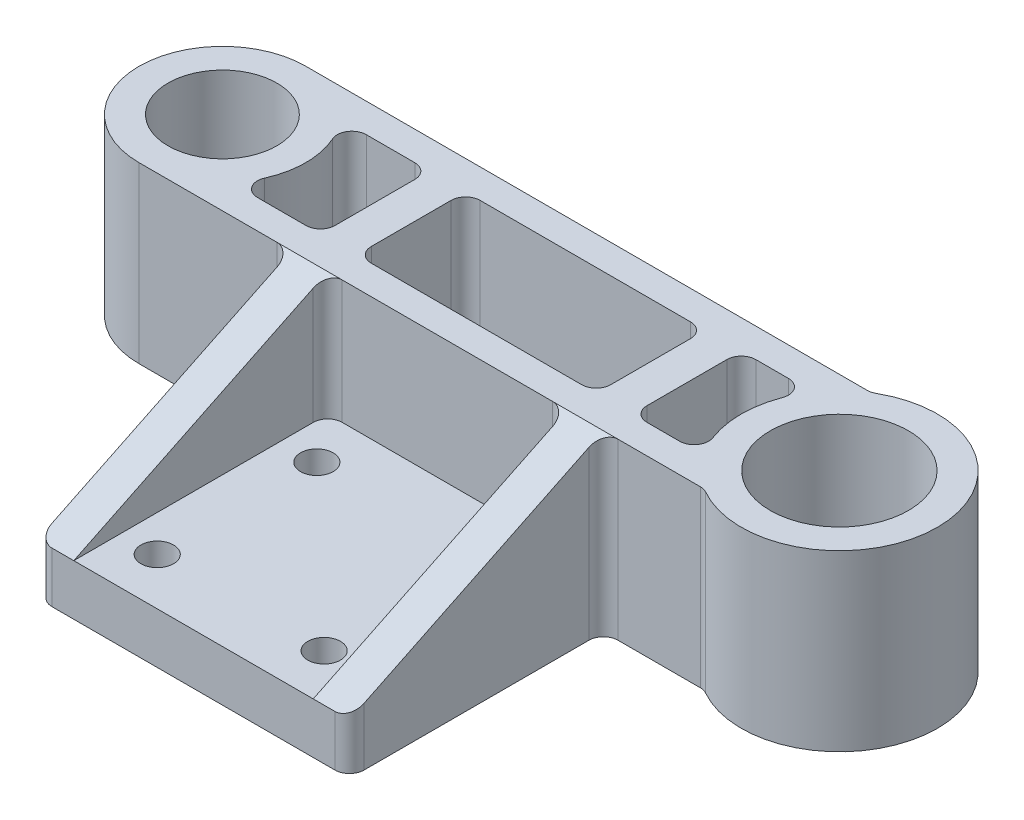
SolidWorks part; units mm, degrees
ref_plane "Front Plane" through (0, 0, 0) normal (0, 0, 1) x (1, 0, 0)
ref_plane "Top Plane" through (0, 0, 0) normal (0, 1, 0) x (1, 0, 0)
ref_plane "Right Plane" through (0, 0, 0) normal (1, 0, 0) x (0, 0, -1)
sketch "Sketch1" plane through (0, 0, 0) normal (0, 1, 0) x (1, 0, 0)
  line L0 (-42.5125, 0) -> (42.5125, 0) construction
  line L1 (-42.5125, 11.5) -> (35.3938, 11.5)
  line L2 (-42.5125, -11.5) -> (35.3938, -11.5)
  circle A0 centre (-42.5125, 0) radius 7.5
  circle A1 centre (42.5125, 0) radius 9.525
  circle A2 centre (-42.5125, 0) radius 11.5
  circle A3 centre (42.5125, 0) radius 13.525
  point P7 (-31.0125, 0)
  point P8 (28.9875, 0)
  dimension "D1" = 15
  dimension "D2" = 19.05
  dimension "D3" = 4
  dimension "D4" = 4
  dimension "D5" = 60
extrude "Boss-Extrude1" add sketch "Sketch1" along normal blind 24
sketch "Sketch8" plane through (0, 0, 11.5) normal (0, 0, 1) x (1, 0, 0)
  line L0 (-42.5125, 0) -> (35.3938, 0) construction
  line L1 (-21.5, 7) -> (21.5, 7)
  line L2 (-21.5, 7) -> (-21.5, 0)
  line L3 (-21.5, 0) -> (21.5, 0)
  line L4 (21.5, 7) -> (21.5, 0)
  line L5 (-21.5, 7) -> (21.5, 0) construction
  line L6 (-21.5, 0) -> (21.5, 7) construction
  line L7 (-42.5125, 24) -> (35.3938, 24) construction
  line L9 (-21.5, 7) -> (-16.5, 7)
  line L10 (-21.5, 7) -> (-21.5, 24)
  line L11 (-21.5, 24) -> (-16.5, 24)
  line L12 (-16.5, 7) -> (-16.5, 24)
  line L13 (21.5, 7) -> (16.5, 7)
  line L14 (21.5, 7) -> (21.5, 24)
  line L15 (21.5, 24) -> (16.5, 24)
  line L16 (16.5, 7) -> (16.5, 24)
  point P0 (0, 3.5)
  point P7 (0, 24)
  line M5 (-42.5125, 0) -> (35.3938, 0)
  line M7 (35.3938, 24) -> (-42.5125, 24)
  dimension "D1" = 7
  dimension "D2" = 43
  dimension "D3" = 5
  dimension "D4" = 5
extrude "Boss-Extrude4" add sketch "Sketch8" along normal blind 35 contours L1 L12 L10 M7 | L4 L1 L2 M5 | L16 L1 L14 M7
sketch "Sketch9" plane through (-21.5, 0, 0) normal (-1, 0, 0) x (0, 0, 1)
  line L0 (11.5, 24) -> (46.5, 7)
  line L1 (46.5, 0) -> (46.5, 24) construction
  line L2 (11.5, 24) -> (46.5, 24)
  line L3 (46.5, 24) -> (46.5, 7)
extrude "Cut-Extrude4" cut sketch "Sketch9" against normal blind 52 and the other way through all
sketch "Sketch10" plane through (0, 24, 0) normal (0, 1, 0) x (1, 0, 0)
  line L0 (-33.7947, 7.5) -> (31.2575, 7.5)
  line L1 (-33.7947, -7.5) -> (31.2575, -7.5)
  line L2 (-42.5125, 11.5) -> (35.3938, 11.5) construction
  line L3 (-16.5, -11.5) -> (16.5, -11.5) construction
  line L4 (-42.5125, -11.5) -> (-21.5, -11.5) construction
  line L5 (-21.5, -46.5) -> (-21.5, -11.5) construction
  line L6 (-21.5, -7.5) -> (-16.5, -7.5)
  line L7 (-21.5, -7.5) -> (-21.5, 7.5)
  line L8 (-21.5, 7.5) -> (-16.5, 7.5)
  line L9 (-16.5, -7.5) -> (-16.5, 7.5)
  line L10 (16.5, -7.5) -> (21.5, -7.5)
  line L11 (16.5, -7.5) -> (16.5, 7.5)
  line L12 (16.5, 7.5) -> (21.5, 7.5)
  line L13 (21.5, -7.5) -> (21.5, 7.5)
  line L14 (-16.5, -46.5) -> (-16.5, -11.5) construction
  line L15 (16.5, -46.5) -> (16.5, -11.5) construction
  line L16 (21.5, -11.5) -> (21.5, -46.5) construction
  circle A0 centre (-42.5125, 0) radius 11.5
  circle A1 centre (42.5125, 0) radius 13.525
  arc A2 (35.3938, -11.5) -> (35.3938, 11.5) centre (42.5125, 0) ccw construction
  arc A3 (-42.5125, 11.5) -> (-42.5125, -11.5) centre (-42.5125, 0) ccw construction
  dimension "D1" = 4
  dimension "D2" = 4
extrude "Cut-Extrude5" cut sketch "Sketch10" against normal blind 35 contours A0 L1 L7 L0 | L1 L11 L0 L9 | A1 L0 L13 L1
fillet "Fillet1" radius 2 20 edges at (35.3938, 12, -11.5) (-16.5, 12, 7.5) (16.5, 12, 7.5) (16.5, 12, -7.5) (-21.5, 12, 11.5) (16.5, 15.5, 11.5) (31.2575, 12, -7.5) (35.3938, 12, 11.5) (21.5, 12, 11.5) (21.5, 12, -7.5) (-21.5, 12, -7.5) (-21.5, 12, 7.5) (-16.5, 15.5, 11.5) (-16.5, 12, -7.5) (-33.7947, 12, -7.5) (-33.7947, 12, 7.5) (21.5, 3.5, 46.5) (-21.5, 3.5, 46.5) (31.2575, 12, 7.5) (21.5, 12, 7.5)
sketch "Sketch12" plane through (0, 0, 0) normal (0, -1, 0) x (1, 0, 0)
  line L0 (-21.5, 44.5) -> (-21.5, 13.5) construction
  line L1 (-11.5, 18) -> (11.5, 18)
  line L2 (-11.5, 18) -> (-11.5, 40)
  line L3 (-11.5, 40) -> (11.5, 40)
  line L4 (11.5, 18) -> (11.5, 40)
  line L5 (-11.5, 18) -> (11.5, 40) construction
  line L6 (-11.5, 40) -> (11.5, 18) construction
  line L7 (-19.5, 46.5) -> (19.5, 46.5) construction
  circle A0 centre (-11.5, 40) radius 2.25
  circle A1 centre (-11.5, 18) radius 2.25
  circle A2 centre (11.5, 40) radius 2.25
  circle A3 centre (11.5, 18) radius 2.25
  point P0 (0, 29)
  point P5 (-21.5, 29)
  point P6 (0, 46.5)
  dimension "D3" = 4.5
  dimension "D4" = 4.5
  dimension "D5" = 4.5
  dimension "D6" = 4.5
  dimension "D1" = 23
  dimension "D2" = 22
extrude "Cut-Extrude6" cut sketch "Sketch12" against normal blind 35 contours A0 | A2 | A3 | A1
